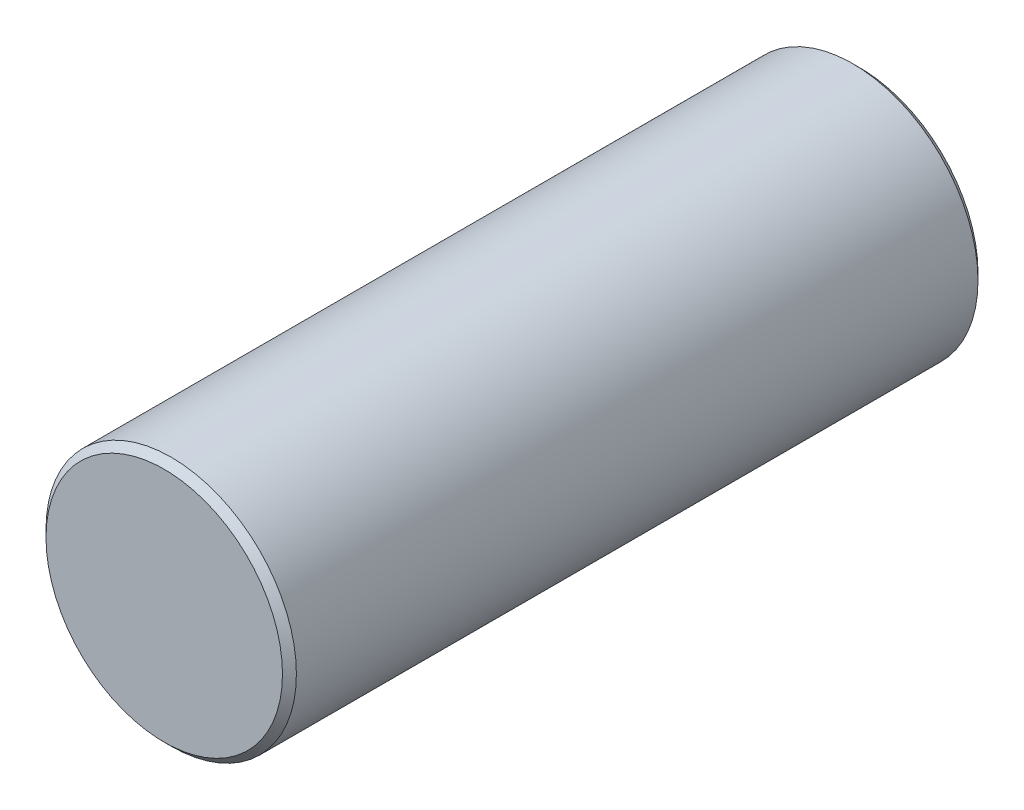
SolidWorks part; units mm, degrees
material "AISI 304"
ref_plane "Front Plane" through (0, 0, 0) normal (0, 0, 1) x (1, 0, 0)
ref_plane "Top Plane" through (0, 0, 0) normal (0, 1, 0) x (1, 0, 0)
ref_plane "Right Plane" through (0, 0, 0) normal (1, 0, 0) x (0, 0, -1)
sketch "Sketch1" plane through (0, 0, 0) normal (1, 0, 0) x (0, 0, -1)
  line L0 (0, 0) -> (35, 0)
  line L1 (35, 0) -> (38, 3)
  line L2 (38, 3) -> (50, 3)
  line L3 (50, 3) -> (50, 9)
  line L4 (50, 9) -> (0, 9)
  line L5 (0, 9) -> (0, 0)
  line L6 (-494.6735, 0) -> (24238.9995, 0) construction
  line L7 (0, -494.6735) -> (0, 24238.9995) construction
  dimension "D1" = 6
  dimension "D2" = 12
  dimension "D3" = 45
  dimension "D4" = 18
  dimension "D5" = 50
revolve "Revolve1" add sketch "Sketch1" angle 360 about L6
chamfer "Chamfer1" distance 0.5 angle 45 3 edges at (9, 0, 0) (3, 0, -50) (9, 0, -50)
